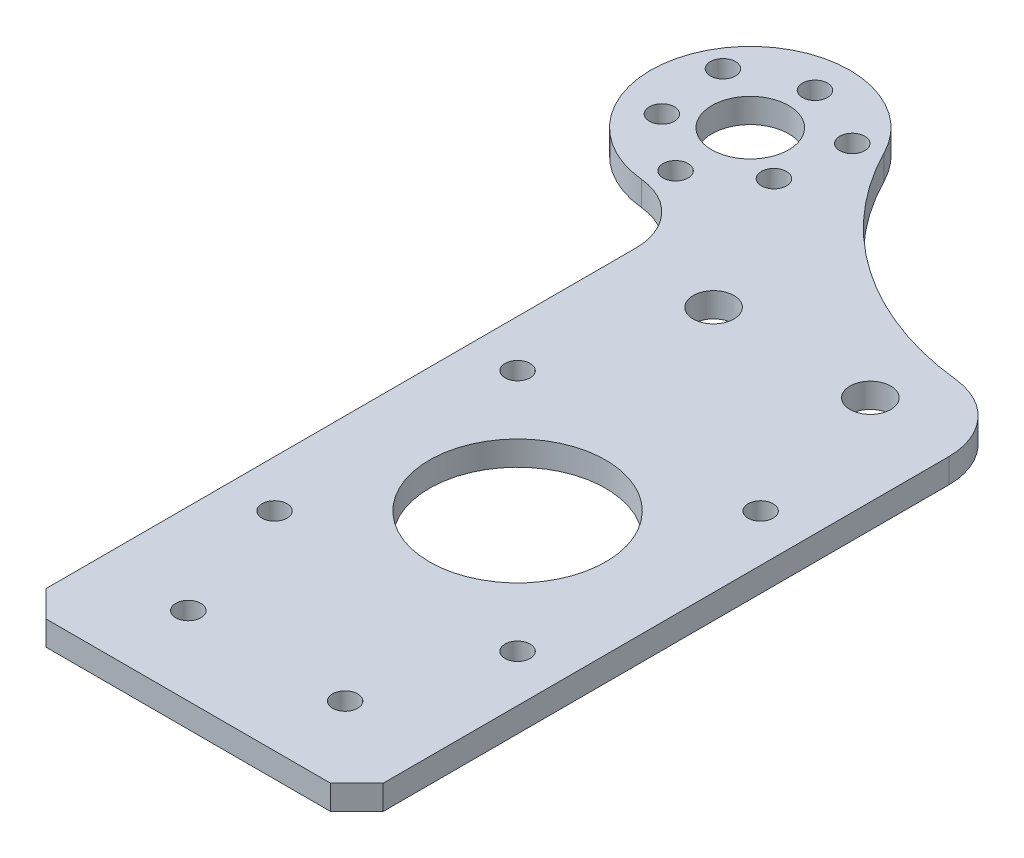
SolidWorks part; units mm, degrees
material "6061-T6 (SS)"
ref_plane "Front Plane" through (0, 0, 0) normal (0, 0, 1) x (1, 0, 0)
ref_plane "Top Plane" through (0, 0, 0) normal (0, 1, 0) x (1, 0, 0)
ref_plane "Right Plane" through (0, 0, 0) normal (1, 0, 0) x (0, 0, -1)
sketch "Sketch1" plane through (0, 0, 0) normal (0, 1, 0) x (1, 0, 0)
  line L0 (-27.5, 86.48) -> (-21.5, 86.48)
  line L1 (-21.5, 3.35) -> (-18.15, 0)
  line L2 (15.5, 57.5) -> (-15.5, 57.5) construction
  line L3 (15.5, 57.5) -> (15.5, 26.5) construction
  line L4 (15.5, 26.5) -> (-15.5, 26.5) construction
  line L5 (-15.5, 57.5) -> (-15.5, 26.5) construction
  line L6 (15.5, 57.5) -> (-15.5, 26.5) construction
  line L7 (15.5, 26.5) -> (-15.5, 57.5) construction
  line L8 (18.15, 0) -> (21.5, 3.35)
  line L193 (0, 0) -> (0, 88.5481) construction
  line L241 (21.5, 75.5175) -> (21.5, 3.35)
  line L244 (-18.15, 0) -> (18.15, 0)
  line L255 (-21.5, 86.48) -> (-21.5, 3.35)
  circle A0 centre (-27.5, 99.18) radius 4.9
  arc A1 (-16.1735, 104.9246) -> (13.4614, 84.466) centre (17.4939, 122) ccw
  circle A2 centre (-27.5, 99.18) radius 8.25 construction
  circle A3 centre (10, 77) radius 2.6
  circle A4 centre (-10, 77) radius 2.6
  circle A5 centre (10, 10) radius 1.6
  circle A6 centre (-10, 10) radius 1.6
  circle A7 centre (-20.3553, 95.055) radius 1.6
  circle A8 centre (-34.6447, 95.055) radius 1.6
  circle A9 centre (-27.5, 107.43) radius 1.6
  arc A10 (-16.1735, 104.9246) -> (-27.5, 86.48) centre (-27.5, 99.18) ccw
  circle A11 centre (0, 42) radius 11.25
  circle A12 centre (-15.5, 26.5) radius 1.6
  circle A13 centre (-15.5, 57.5) radius 1.6
  circle A14 centre (15.5, 57.5) radius 1.6
  circle A15 centre (15.5, 26.5) radius 1.6
  arc A16 (13.4614, 84.466) -> (21.5, 75.5175) centre (12.5, 75.5175) cw
  point P15 (21.5, 0)
  point P16 (-21.5, 0)
  point P24 (0, 42)
  point P30 (-27.5, 99.18)
  dimension "D7" = 5.2
  dimension "D2" = 3.2
  dimension "D17" = 22.5
  dimension "D10" = 25.4
  dimension "D13" = 37.75
  dimension "D19" = 9.8
  dimension "D20" = 16.5
  dimension "D21" = 9
  dimension "D5" = 20
  dimension "D6" = 10
  dimension "D8" = 77
  dimension "D9" = 20
  dimension "D14" = 27.5
  dimension "D4" = 42
  dimension "D15" = 31
  dimension "D16" = 43
  dimension "D12" = 122
  dimension "D22" = 3.35
  dimension "D23" = 3.35
  dimension "D24" = 3.35
  dimension "D25" = 3.35
  dimension "D11" = 22.18
  dimension "D3" = 4
  dimension "D18" = 3
extrude "Boss-Extrude1" add sketch "Sketch1" along normal blind 3.125
sketch "Sketch2" plane through (0, 3.125, 0) normal (0, 1, 0) x (1, 0, 0)
  line L0 (10, 77) -> (-10, 77) construction
  line L2 (-31.1681, 59.8462) -> (-31.4022, 59.8708) construction
ref_plane "Plane1" through (0, 0, -77) normal (0, 0, -1) x (-1, 0, 0)
fillet "Fillet1" radius 8 1 edges at (-21.5, 1.5625, -86.48)
sketch "Sketch3" plane through (0, 3.125, 0) normal (0, 1, 0) x (1, 0, 0)
  circle A0 centre (-27.5, 99.18) radius 9.5263 construction
  circle A1 centre (-27.5, 89.6537) radius 1.6
  circle A2 centre (-35.75, 103.9431) radius 1.6
  circle A3 centre (-19.25, 103.9431) radius 1.6
  point P12 (-27.5, 99.18)
  dimension "D1" = 3.2
  dimension "D3" = 16.5
  dimension "D2" = 3
extrude "Cut-Extrude1" cut sketch "Sketch3" against normal up to next
equation "\"D23@Sketch1\"=\"D22@Sketch1\""
equation "\"D24@Sketch1\"=\"D22@Sketch1\""
equation "\"D25@Sketch1\"=\"D22@Sketch1\""
